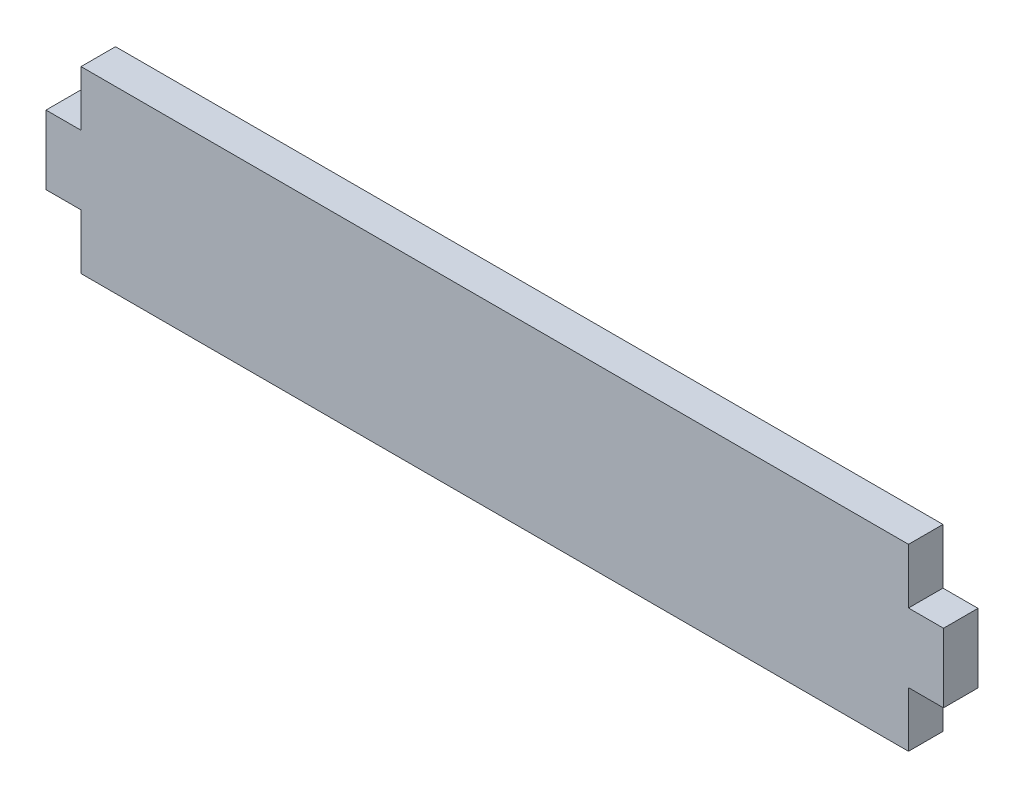
SolidWorks part; units mm, degrees
ref_plane "Front Plane" through (0, 0, 0) normal (0, 0, 1) x (1, 0, 0)
ref_plane "Top Plane" through (0, 0, 0) normal (0, 1, 0) x (1, 0, 0)
ref_plane "Right Plane" through (0, 0, 0) normal (1, 0, 0) x (0, 0, -1)
sketch "Sketch1" plane through (0, 0, 0) normal (0, 0, 1) x (1, 0, 0)
  line L1 (-38.1, -8.255) -> (38.1, -8.255)
  line L2 (-38.1, -8.255) -> (-38.1, 8.255)
  line L3 (-38.1, 8.255) -> (38.1, 8.255)
  line L4 (38.1, -8.255) -> (38.1, 8.255)
  line L5 (-38.1, -8.255) -> (38.1, 8.255) construction
  line L6 (-38.1, 8.255) -> (38.1, -8.255) construction
  point P0 (0, 0)
  dimension "D1" = 76.2
  dimension "D2" = 16.51
extrude "Boss-Extrude1" add sketch "Sketch1" along normal blind 3.175
sketch "Sketch3" plane through (0, 0, 3.175) normal (0, 0, 1) x (1, 0, 0)
  line L0 (-38.1, 0) -> (-28.4093, 0) construction
  line L2 (-38.1, 8.255) -> (-38.1, -8.255) construction
  line L3 (-38.1, 0) -> (-38.1, 3.175)
  line L4 (-38.1, 3.175) -> (-41.3258, 3.175)
  line L5 (-41.3258, 3.175) -> (-41.3258, -3.175)
  line L6 (-41.3258, -3.175) -> (-38.1, -3.175)
  line L7 (-38.1, -3.175) -> (-38.1, 0)
  dimension "D1" = 6.35
  dimension "D2" = 3.2258
extrude "Boss-Extrude2" add sketch "Sketch3" against normal blind 3.175
mirror "Mirror2" about plane through (0, 0, 0) normal (1, 0, 0) of "Boss-Extrude2"
